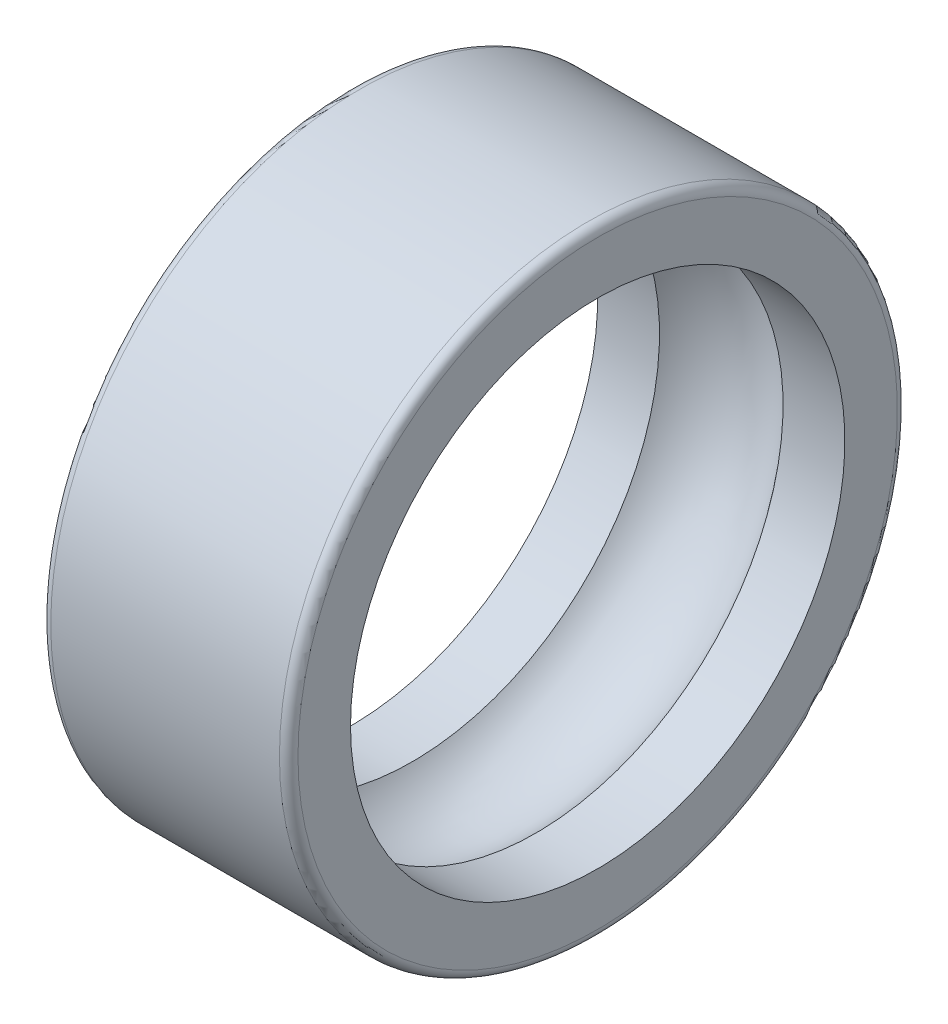
SolidWorks part; units mm, degrees
ref_plane "Plan1" through (0, 0, 0) normal (0, 0, 1) x (1, 0, 0)
ref_plane "Plan2" through (0, 0, 0) normal (0, 1, 0) x (1, 0, 0)
ref_plane "Plan3" through (0, 0, 0) normal (1, 0, 0) x (0, 0, -1)
sketch "Esquisse1" plane through (0, 0, 0) normal (0, 0, 1) x (1, 0, 0)
  line L0 (0, 4) -> (1, 4) construction
  line L1 (0, 4) -> (0, 5) construction
  line L2 (0, 5) -> (4, 5) construction
  line L3 (4, 4) -> (4, 5) construction
  line L4 (3, 4) -> (4, 4) construction
  line L5 (0, 4) -> (1, 4)
  line L6 (0, 4) -> (0, 5)
  line L7 (0, 5) -> (4, 5)
  line L8 (4, 4) -> (4, 5)
  line L9 (3, 4) -> (4, 4)
  line L10 (0, 0) -> (5.2157, 0) construction
  line L11 (0, 0) -> (7.3387, 0) construction
  circle A0 centre (2, 3.25) radius 1.25 construction
  arc A1 (3, 4) -> (1, 4) centre (2, 3.25) ccw
revolve "Base-Révolution" add sketch "Esquisse1" angle 360 about L10
fillet "Congé1" radius 0.15
